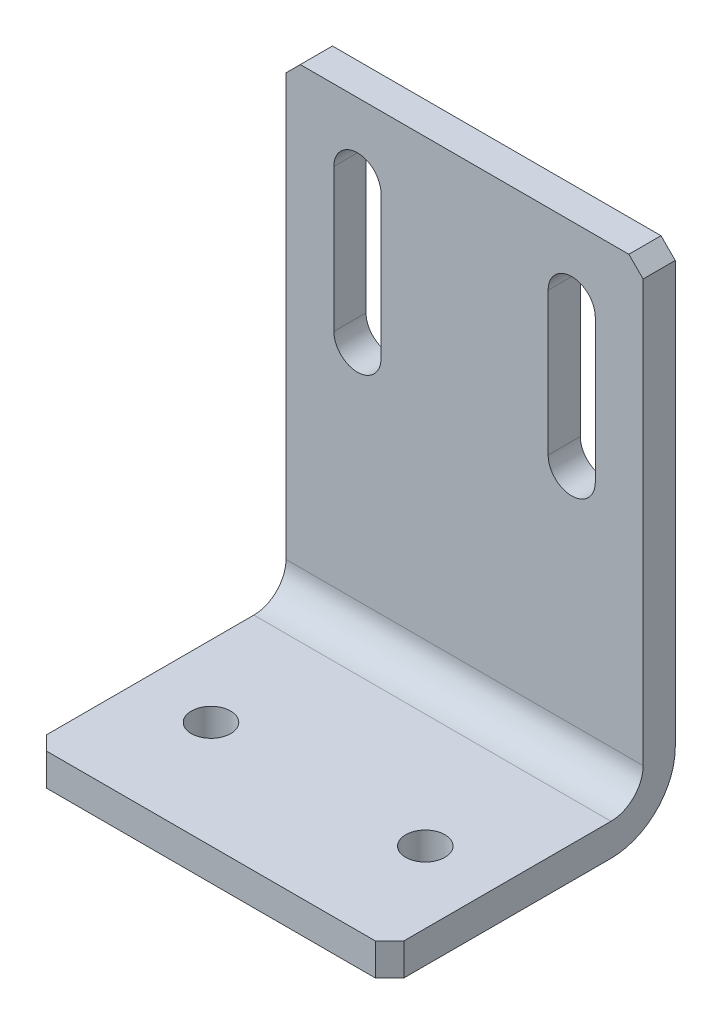
SolidWorks part; units mm, degrees
ref_plane "Front" through (0, 0, 0) normal (0, 0, 1) x (1, 0, 0)
ref_plane "Top" through (0, 0, 0) normal (0, 1, 0) x (1, 0, 0)
ref_plane "Right" through (0, 0, 0) normal (1, 0, 0) x (0, 0, -1)
sketch "Sketch1" plane through (0, 0, 0) normal (1, 0, 0) x (0, 0, -1)
  line L1 (0, 0) -> (-40, 0)
  line L2 (0, 0) -> (0, 70)
  line L3 (0, 70) -> (-4.5, 70)
  line L4 (-40, 0) -> (-40, 4.5)
  line L5 (-4.5, 4.5) -> (-40, 4.5)
  line L6 (-4.5, 4.5) -> (-4.5, 70)
  point P11 (0, 0)
  dimension "D1" = 4.5
  dimension "D2" = 4.5
  dimension "D3" = 40
  dimension "D4" = 70
extrude "Boss-Extrude1" add sketch "Sketch1" along normal mid plane 50
fillet "Fillet1" radius 4.5 1 edges at (0, 4.5, 4.5)
fillet "Fillet2" radius 9 1 edges at (0, 0, 0)
hole_wizard "M5 Clearance Hole1" positions "Sketch3" profile "Sketch2" hole size "M5" standard "JIS" end condition through all
sketch "Sketch3" plane through (0, 4.5, 0) normal (0, 1, 0) x (-1, 0, 0)
  line L1 (-25, 40) -> (25, 40) construction
  line L2 (0, 42.7636) -> (0, -3.0702) construction
  line L4 (-25, 9) -> (-25, 40) construction
  line L5 (25, 9) -> (25, 40) construction
  point P0 (15, 25)
  point P1 (-15, 25)
  dimension "D1" = 10
  dimension "D2" = 15
  dimension "D3" = 30
  dimension "D4" = 10
sketch "Sketch2" plane through (-15, 4.5, 25) normal (1, 0, 0) x (0, 0, 1)
  line L0 (0, 0) -> (0, 4.5)
  line L1 (0, 4.5) -> (2.75, 4.5)
  line L2 (2.75, 4.5) -> (2.75, 0)
  line L5 (2.75, 0) -> (0, 0)
  line L11 (0, -6.35) -> (0, 107.95) construction
  dimension "通し穴の直径" = 5.5
  dimension "通し穴の深さ" = 4.5
sketch "Sketch4" plane through (0, 0, 4.5) normal (0, 0, 1) x (1, 0, 0)
  line L0 (-15, 60) -> (-15, 40) construction
  line L1 (-11.7, 60) -> (-11.7, 40)
  line L2 (-18.3, 60) -> (-18.3, 40)
  line L3 (15, 60) -> (15, 40) construction
  line L4 (18.3, 60) -> (18.3, 40)
  line L5 (11.7, 60) -> (11.7, 40)
  line L7 (25, 70) -> (-25, 70) construction
  line L8 (0, -5.7063) -> (0, 76.9645) construction
  line L9 (25, 70) -> (25, 9) construction
  line L10 (-25, 70) -> (-25, 9) construction
  arc A0 (-11.7, 60) -> (-18.3, 60) centre (-15, 60) ccw
  arc A1 (-18.3, 40) -> (-11.7, 40) centre (-15, 40) ccw
  arc A2 (18.3, 60) -> (11.7, 60) centre (15, 60) ccw
  arc A3 (11.7, 40) -> (18.3, 40) centre (15, 40) ccw
  point P2 (-15, 50)
  point P9 (15, 50)
  dimension "D1" = 3.3
  dimension "D5" = 26.6
  dimension "D2" = 30
  dimension "D3" = 10
  dimension "D4" = 20
  dimension "D6" = 10
extrude "Cut-Extrude1" cut sketch "Sketch4" against normal through all
chamfer "Chamfer1" distance 2 angle 45 4 edges at (-25, 2.25, 40) (25, 2.25, 40) (25, 70, 2.25) (-25, 70, 2.25)
